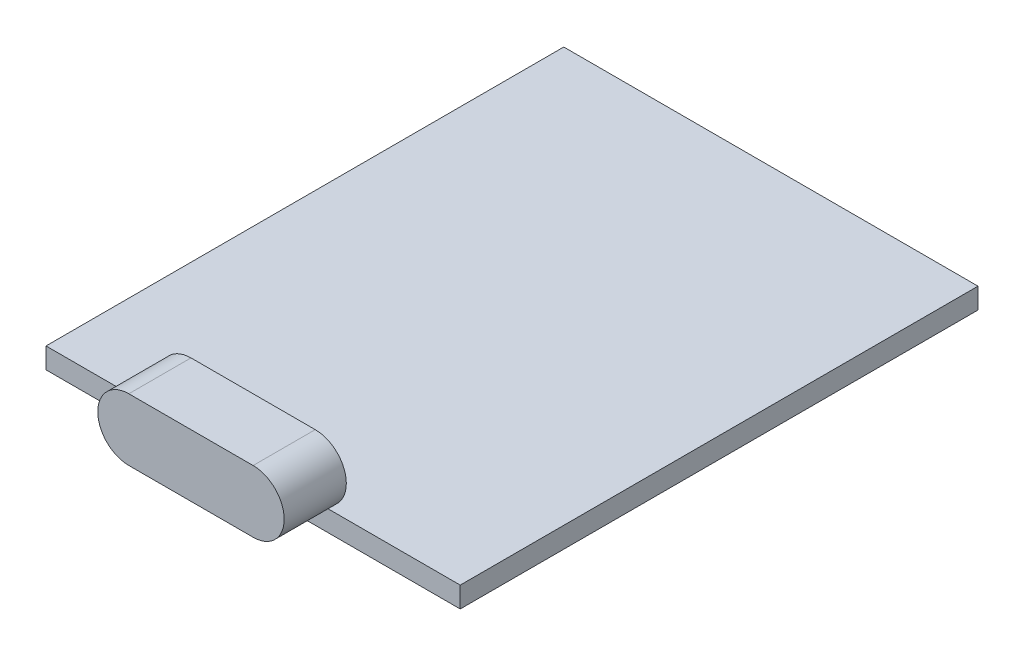
SolidWorks part; units mm, degrees
material "1023 Carbon Steel Sheet (SS)"
ref_plane "Front Plane" through (0, 0, 0) normal (0, 0, 1) x (1, 0, 0)
ref_plane "Top Plane" through (0, 0, 0) normal (0, 1, 0) x (1, 0, 0)
ref_plane "Right Plane" through (0, 0, 0) normal (1, 0, 0) x (0, 0, -1)
sketch "Sketch1" plane through (0, 0, 0) normal (0, 1, 0) x (1, 0, 0)
  line L1 (10, -12.5) -> (-10, -12.5)
  line L2 (10, -12.5) -> (10, 12.5)
  line L3 (10, 12.5) -> (-10, 12.5)
  line L4 (-10, -12.5) -> (-10, 12.5)
  line L5 (10, -12.5) -> (-10, 12.5) construction
  line L6 (10, 12.5) -> (-10, -12.5) construction
  point P0 (0, 0)
  dimension "D1" = 25
  dimension "D2" = 20
extrude "Boss-Extrude1" add sketch "Sketch1" along normal blind 1
sketch "Sketch2" plane through (0, 0, 12.5) normal (0, 0, 1) x (1, 0, 0)
  line L0 (0, 0) -> (0, 5)
  line L1 (-3, 2.5) -> (3, 2.5) construction
  line L2 (-3, 4) -> (3, 4)
  line L3 (-3, 1) -> (3, 1)
  line L4 (-10, 0) -> (10, 0)
  line L5 (10, 0) -> (10, 1)
  line L6 (10, 1) -> (-10, 1)
  line L7 (-10, 1) -> (-10, 0)
  line L8 (-10, 0) -> (10, 0)
  line L9 (10, 0) -> (10, 1)
  line L10 (10, 1) -> (-10, 1)
  line L11 (-10, 1) -> (-10, 0)
  arc A0 (-3, 4) -> (-3, 1) centre (-3, 2.5) ccw
  arc A1 (3, 1) -> (3, 4) centre (3, 2.5) ccw
  point P8 (0, 2.5)
  dimension "D3" = 6
  dimension "D2" = 3
  dimension "D4" = 1.5
  dimension "D1" = 0
extrude "Boss-Extrude2" add sketch "Sketch2" along normal blind 3 separate body
